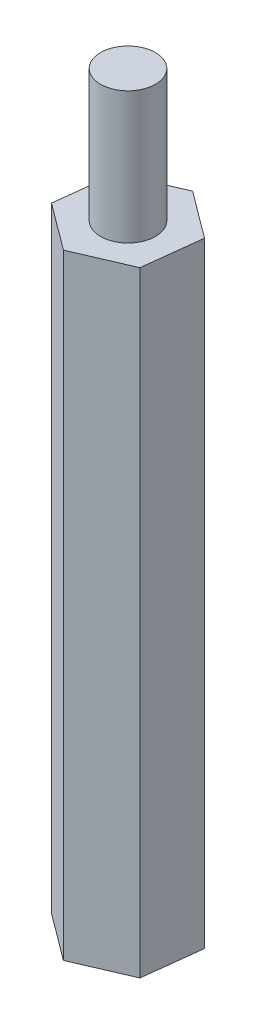
SolidWorks part; units mm, degrees
ref_plane "前视基准面" through (0, 0, 0) normal (0, 0, 1) x (1, 0, 0)
ref_plane "上视基准面" through (0, 0, 0) normal (0, 1, 0) x (1, 0, 0)
ref_plane "右视基准面" through (0, 0, 0) normal (1, 0, 0) x (0, 0, -1)
sketch "草图1" plane through (0, 0, 0) normal (0, 1, 0) x (1, 0, 0)
  line L1 (2.1251, -1.5831) -> (2.4336, 1.0488)
  line L2 (2.4336, 1.0488) -> (0.3085, 2.632)
  line L3 (0.3085, 2.632) -> (-2.1251, 1.5831)
  line L4 (-2.1251, 1.5831) -> (-2.4336, -1.0488)
  line L5 (-2.4336, -1.0488) -> (-0.3085, -2.632)
  line L6 (-0.3085, -2.632) -> (2.1251, -1.5831)
  circle A0 centre (0, 0) radius 2.295 construction
  dimension "D1" = 5.3
extrude "凸台-拉伸1" add sketch "草图1" along normal blind 28
sketch "草图2" plane through (0, 28, 0) normal (0, 1, 0) x (1, 0, 0)
  line L6 (-0.3085, -2.632) -> (2.1251, -1.5831)
  line L7 (2.1251, -1.5831) -> (2.4336, 1.0488)
  line L8 (2.4336, 1.0488) -> (0.3085, 2.632)
  line L9 (0.3085, 2.632) -> (-2.1251, 1.5831)
  line L10 (-2.1251, 1.5831) -> (-2.4336, -1.0488)
  line L11 (-2.4336, -1.0488) -> (-0.3085, -2.632)
  line L12 (-0.3085, -2.632) -> (2.1251, -1.5831)
  line L13 (2.1251, -1.5831) -> (2.4336, 1.0488)
  line L14 (2.4336, 1.0488) -> (0.3085, 2.632)
  line L15 (0.3085, 2.632) -> (-2.1251, 1.5831)
  line L16 (-2.1251, 1.5831) -> (-2.4336, -1.0488)
  line L17 (-2.4336, -1.0488) -> (-0.3085, -2.632)
  circle A0 centre (0, 0) radius 1.25
  dimension "D2" = 2.5
  dimension "D1" = 0
extrude "凸台-拉伸2" add sketch "草图2" along normal blind 6 contours A0
sketch "草图3" plane through (0, 0, 0) normal (0, -1, 0) x (1, 0, 0)
  line L6 (2.1251, 1.5831) -> (-0.3085, 2.632)
  line L7 (-0.3085, 2.632) -> (-2.4336, 1.0488)
  line L8 (-2.4336, 1.0488) -> (-2.1251, -1.5831)
  line L9 (-2.1251, -1.5831) -> (0.3085, -2.632)
  line L10 (0.3085, -2.632) -> (2.4336, -1.0488)
  line L11 (2.4336, -1.0488) -> (2.1251, 1.5831)
  line L12 (2.1251, 1.5831) -> (-0.3085, 2.632)
  line L13 (-0.3085, 2.632) -> (-2.4336, 1.0488)
  line L14 (-2.4336, 1.0488) -> (-2.1251, -1.5831)
  line L15 (-2.1251, -1.5831) -> (0.3085, -2.632)
  line L16 (0.3085, -2.632) -> (2.4336, -1.0488)
  line L17 (2.4336, -1.0488) -> (2.1251, 1.5831)
  circle A0 centre (0, 0) radius 1.25
  dimension "D2" = 2.5
  dimension "D1" = 0
extrude "切除-拉伸1" cut sketch "草图3" against normal blind 6 contours A0
